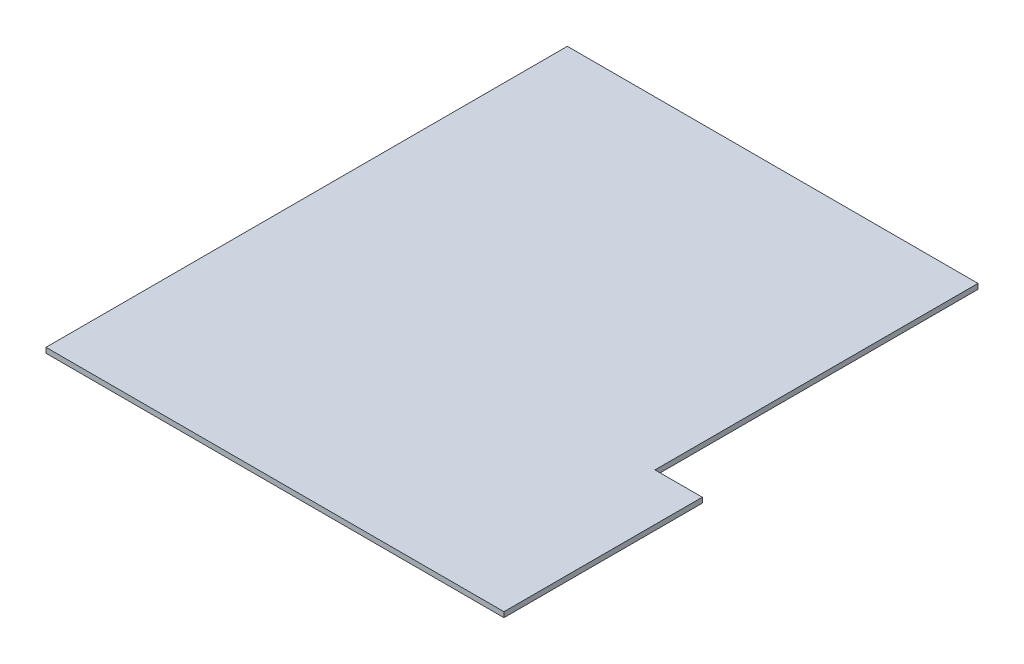
SolidWorks part; units mm, degrees
ref_plane "Front Plane" through (0, 0, 0) normal (0, 0, 1) x (1, 0, 0)
ref_plane "Top Plane" through (0, 0, 0) normal (0, 1, 0) x (1, 0, 0)
ref_plane "Right Plane" through (0, 0, 0) normal (1, 0, 0) x (0, 0, -1)
sketch "Sketch1" plane through (0, 0, 0) normal (0, 1, 0) x (1, 0, 0)
  line L2 (9680, 0) -> (9680, 4191.8)
  line L5 (8680, 11020) -> (0, 11020)
  line L12 (0, 11020) -> (0, 0)
  line L13 (8680, 11020) -> (8680, 4191.8)
  line L14 (8680, 4191.8) -> (9680, 4191.8)
  line L15 (0, 0) -> (9680, 0)
extrude "Boss-Extrude3" add sketch "Sketch1" along normal blind 110
sketch "Sketch2" plane through (0, 110, 0) normal (0, 1, 0) x (1, 0, 0)
  line L1 (0, 0) -> (9680, 0) construction
  line L2 (4140, 0) -> (4140, 159.61)
  line L3 (4140, 159.61) -> (5540, 159.61)
  line L4 (5540, 159.61) -> (5540, 0)
